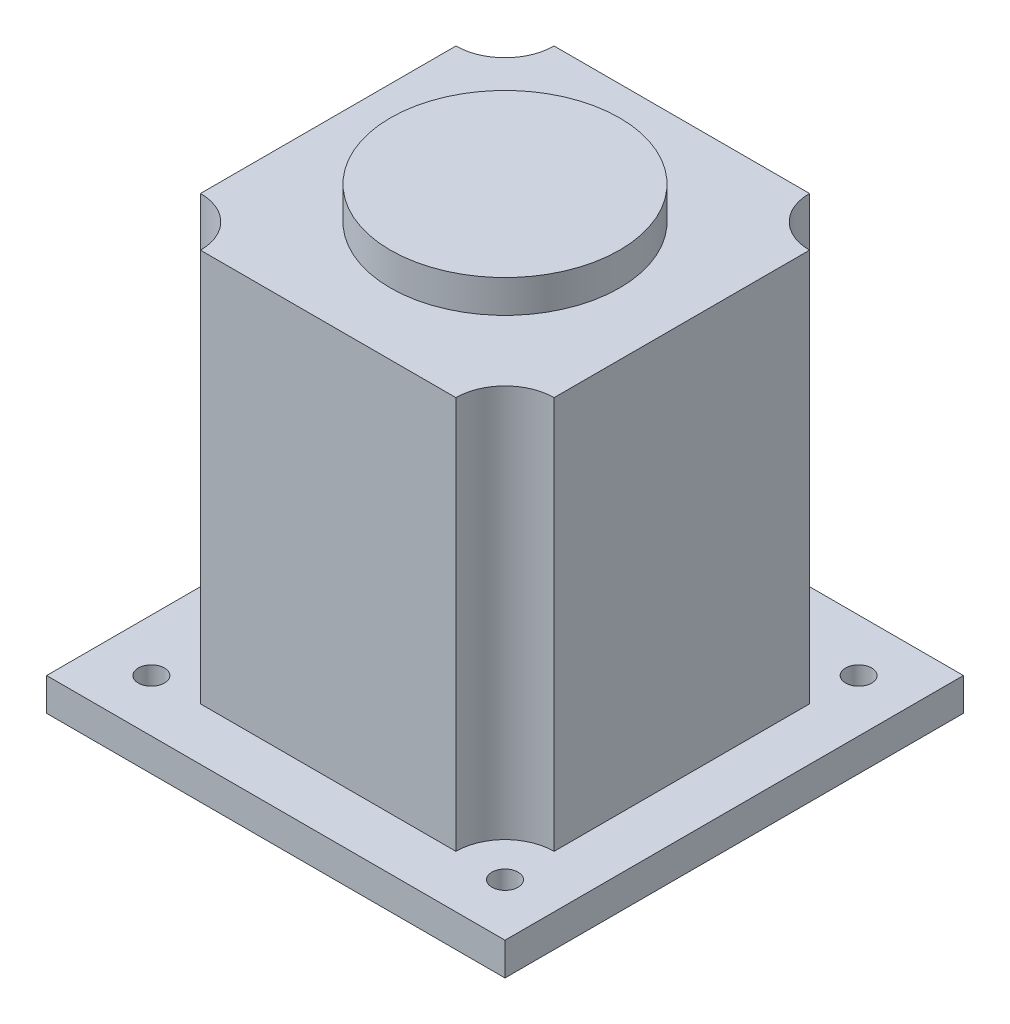
SolidWorks part; units mm, degrees
ref_plane "前视基准面" through (0, 0, 0) normal (0, 0, 1) x (1, 0, 0)
ref_plane "上视基准面" through (0, 0, 0) normal (0, 1, 0) x (1, 0, 0)
ref_plane "右视基准面" through (0, 0, 0) normal (1, 0, 0) x (0, 0, -1)
sketch "草图1" plane through (0, 0, 0) normal (0, 1, 0) x (1, 0, 0)
  line L1 (70, -70) -> (-70, -70)
  line L2 (70, -70) -> (70, 70)
  line L3 (70, 70) -> (-70, 70)
  line L4 (-70, -70) -> (-70, 70)
  line L5 (70, -70) -> (-70, 70) construction
  line L6 (70, 70) -> (-70, -70) construction
  line L7 (54, -54) -> (-54, -54) construction
  line L8 (54, -54) -> (54, 54) construction
  line L9 (54, 54) -> (-54, 54) construction
  line L10 (-54, -54) -> (-54, 54) construction
  line L11 (54, -54) -> (-54, 54) construction
  line L12 (54, 54) -> (-54, -54) construction
  circle A0 centre (54, 54) radius 4
  circle A1 centre (54, -54) radius 4
  circle A2 centre (-54, -54) radius 4
  circle A3 centre (-54, 54) radius 4
  point P0 (0, 0)
  point P6 (0, 0)
  dimension "D3" = 8
  dimension "D1" = 140
  dimension "D2" = 108
extrude "凸台-拉伸1" add sketch "草图1" along normal blind 10
sketch "草图2" plane through (0, 10, 0) normal (0, 1, 0) x (1, 0, 0)
  line L1 (39, 54) -> (-39, 54)
  line L2 (54, 39) -> (54, -39)
  line L3 (39, -54) -> (-39, -54)
  line L4 (-54, 39) -> (-54, -39)
  line L5 (43.3934, 43.3934) -> (-43.3934, -43.3934) construction
  line L6 (43.3934, -43.3934) -> (-43.3934, 43.3934) construction
  arc A0 (-54, 39) -> (-39, 54) centre (-54, 54) ccw
  arc A1 (39, 54) -> (54, 39) centre (54, 54) ccw
  arc A2 (54, -39) -> (39, -54) centre (54, -54) ccw
  arc A3 (-39, -54) -> (-54, -39) centre (-54, -54) ccw
  point P0 (0, 0)
  dimension "D1" = 30
extrude "凸台-拉伸2" add sketch "草图2" along normal blind 120
sketch "草图3" plane through (0, 130, 0) normal (0, 1, 0) x (1, 0, 0)
  circle A0 centre (0, 0) radius 35
  dimension "D1" = 70
extrude "凸台-拉伸3" add sketch "草图3" along normal blind 10
sketch "草图4" plane through (0, 0, 0) normal (0, -1, 0) x (1, 0, 0)
  circle A0 centre (0, 0) radius 8
  dimension "D1" = 16
extrude "凸台-拉伸4" add sketch "草图4" along normal blind 5
